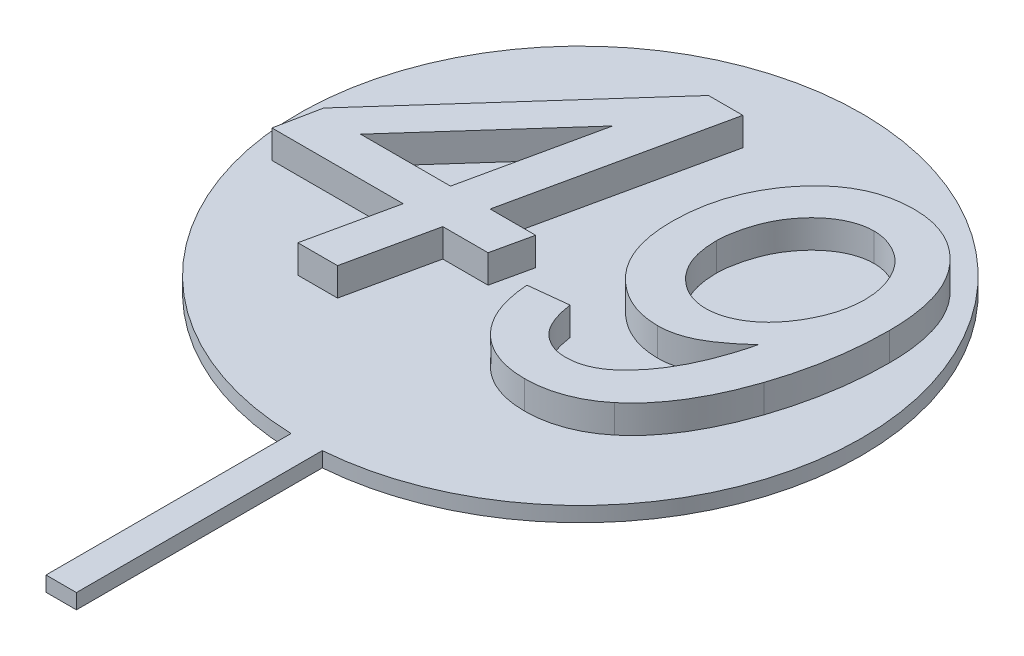
SolidWorks part; units mm, degrees
ref_plane "Спереди" through (0, 0, 0) normal (0, 0, 1) x (1, 0, 0)
ref_plane "Сверху" through (0, 0, 0) normal (0, 1, 0) x (1, 0, 0)
ref_plane "Справа" through (0, 0, 0) normal (1, 0, 0) x (0, 0, -1)
other "Configuration Table"
sketch "Эскиз1" plane through (0, 0, 0) normal (0, 1, 0) x (1, 0, 0)
  circle A0 centre (0, 0) radius 30
  dimension "D1" = 60
extrude "Бобышка-Вытянуть1" add sketch "Эскиз1" along normal blind 1.6
sketch "Эскиз2" plane through (0, 1.6, 0) normal (0, 1, 0) x (1, 0, 0)
  text T0 "49" font "Arial" height in points 140
extrude "Бобышка-Вытянуть2" add sketch "Эскиз2" along normal blind 3
sketch "Эскиз3" plane through (0, 0, 0) normal (0, -1, 0) x (1, 0, 0)
  line L1 (-0.8573, 56.1241) -> (2.387, 56.1241)
  line L2 (-0.8573, 56.1241) -> (-0.8573, 20.8501)
  line L3 (-0.8573, 20.8501) -> (2.387, 20.8501)
  line L4 (2.387, 56.1241) -> (2.387, 20.8501)
  line L5 (0.7649, 20.8501) -> (0.7649, 56.1241) construction
  line L6 (-0.8573, 38.4871) -> (2.387, 38.4871) construction
  point P528 (0.7649, 38.4871)
extrude "Бобышка-Вытянуть5" add sketch "Эскиз3" against normal blind 1.6 contours L2 L3 L4 L1
